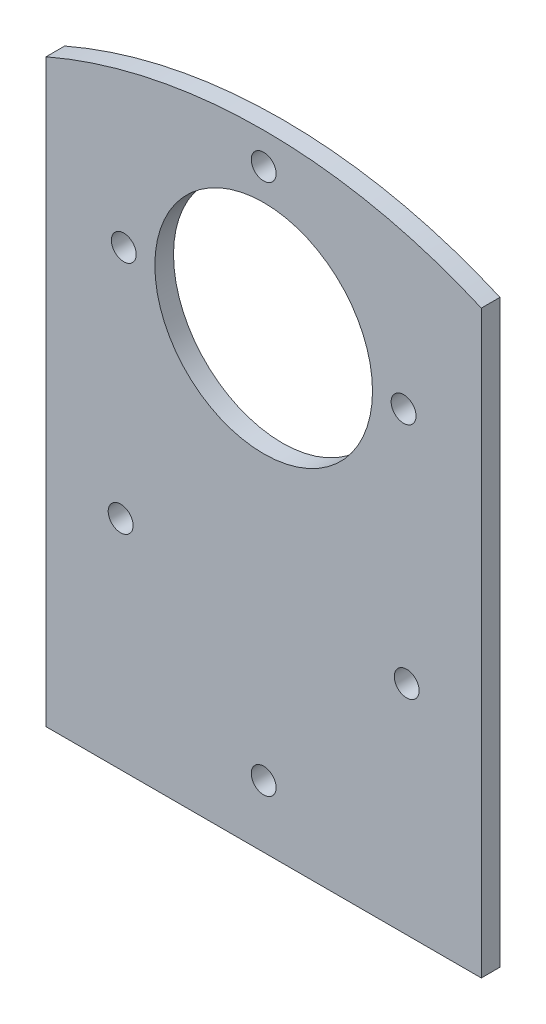
SolidWorks part; units mm, degrees
material "6061 Alloy"
ref_plane "Front Plane" through (0, 0, 0) normal (0, 0, 1) x (1, 0, 0)
ref_plane "Top Plane" through (0, 0, 0) normal (0, 1, 0) x (1, 0, 0)
ref_plane "Right Plane" through (0, 0, 0) normal (1, 0, 0) x (0, 0, -1)
sketch "Sketch1" plane through (0, 0, 0) normal (0, 0, 1) x (1, 0, 0)
  line L1 (35, -52.5) -> (-35, -52.5)
  line L2 (35, -52.5) -> (35, 52.5)
  line L3 (35, 52.5) -> (-35, 52.5)
  line L4 (-35, -52.5) -> (-35, 52.5)
  line L5 (35, -52.5) -> (-35, 52.5) construction
  line L6 (35, 52.5) -> (-35, -52.5) construction
  point P0 (0, 0)
  dimension "D1" = 70
  dimension "D2" = 105
extrude "Boss-Extrude1" add sketch "Sketch1" along normal blind 3
sketch "Sketch2" plane through (0, 0, 0) normal (0, 0, -1) x (-1, 0, 0)
  line L0 (-35, -2.5) -> (35, -2.5) construction
  line L1 (-35, -52.5) -> (-35, 52.5) construction
  line L2 (35, 52.5) -> (35, -52.5) construction
  line L3 (35, -52.5) -> (-35, -52.5) construction
  circle A0 centre (0, 20.5) radius 17.5
  point P11 (0, -2.5)
  dimension "D2" = 35
  dimension "D1" = 50
  dimension "D3" = 23
  dimension "D4" = 35
extrude "Cut-Extrude3" cut sketch "Sketch2" against normal blind 3
sketch "Sketch3" plane through (0, 0, 3) normal (0, 0, 1) x (1, 0, 0)
  circle A5 centre (0, 20.5) radius 17.5 construction
  circle A6 centre (-22.5, 20.5) radius 2
  circle A7 centre (0, 43) radius 2
  circle A8 centre (22.5, 20.5) radius 2
  point P0 (0, 20.5)
  dimension "D2" = 22.5
  dimension "D3" = 22.5
  dimension "D4" = 4
  dimension "D5" = 4
  dimension "D6" = 4
  dimension "D1" = 22.5
extrude "Cut-Extrude4" cut sketch "Sketch3" against normal blind 3
sketch "Sketch4" plane through (0, 0, 3) normal (0, 0, 1) x (1, 0, 0)
  line L0 (0, 0) -> (0, -52.5) construction
  line L1 (-35, -52.5) -> (35, -52.5) construction
  circle A0 centre (0, -42.5) radius 2
  circle A1 centre (-23, -17.5) radius 2
  circle A3 centre (23, -17.5) radius 2
  dimension "D3" = 4
  dimension "D1" = 10
  dimension "D2" = 25
  dimension "D4" = 23
extrude "Cut-Extrude5" cut sketch "Sketch4" against normal blind 5
sketch "Sketch5" plane through (0, 0, 3) normal (0, 0, 1) x (1, 0, 0)
  line L0 (-35, 40.7935) -> (35, 40.7935) construction
  line L1 (-35, 52.5) -> (-35, -52.5) construction
  line L2 (35, -52.5) -> (35, 52.5) construction
  line L3 (-35, 40.7935) -> (-35, 52.5)
  line L4 (-35, 52.5) -> (35, 52.5)
  line L5 (35, 52.5) -> (35, 40.7935)
  arc A0 (-35, 40.7935) -> (35, 40.7935) centre (0, -39.6661) cw
extrude "Cut-Extrude6" cut sketch "Sketch5" against normal blind 10
